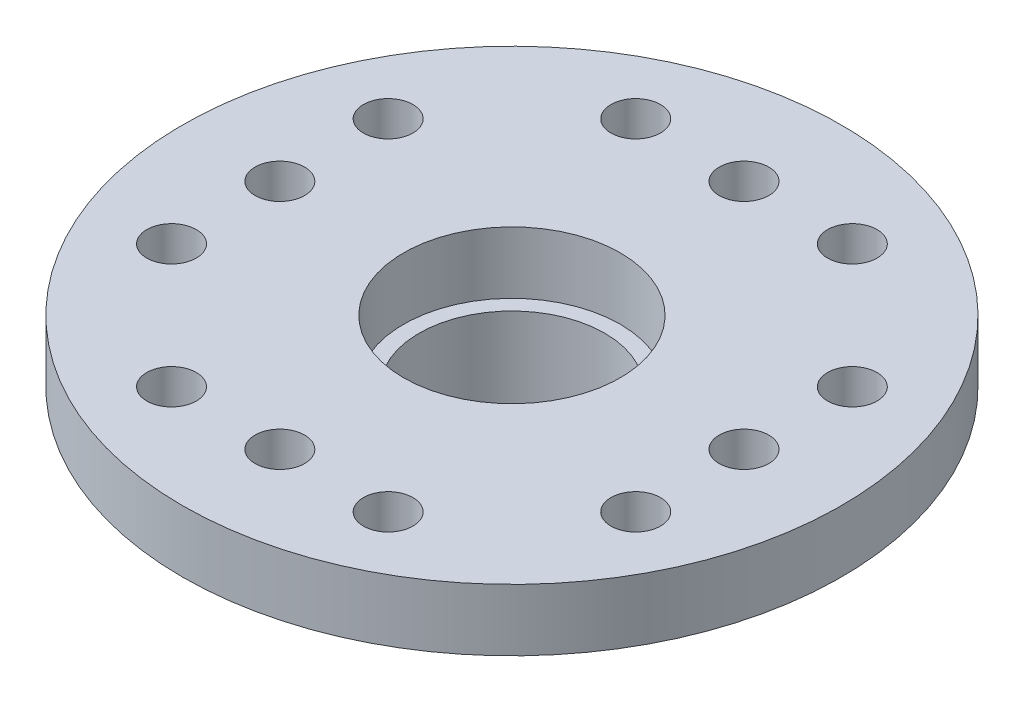
SolidWorks part; units mm, degrees
ref_plane "Спереди" through (0, 0, 0) normal (0, 0, 1) x (1, 0, 0)
ref_plane "Сверху" through (0, 0, 0) normal (0, 1, 0) x (1, 0, 0)
ref_plane "Справа" through (0, 0, 0) normal (1, 0, 0) x (0, 0, -1)
sketch "Эскиз1" plane through (0, 0, 0) normal (0, 1, 0) x (1, 0, 0)
  circle A0 centre (0, 0) radius 10.65
  circle A1 centre (0, 0) radius 3.5
  dimension "D1" = 21.3
  dimension "D2" = 7
extrude "Бобышка-Вытянуть1" add sketch "Эскиз1" along normal blind 2
sketch "Эскиз2" plane through (0, 0, 0) normal (0, -1, 0) x (1, 0, 0)
  circle A0 centre (0, 0) radius 4.3
  circle A1 centre (0, 0) radius 3
  dimension "D1" = 8.6
  dimension "D2" = 6
extrude "Бобышка-Вытянуть2" add sketch "Эскиз2" along normal blind 3.8
fillet "Скругление1" radius 1 1 edges at (0, 0, 4.3)
sketch "Эскиз3" plane through (0, 2, 0) normal (0, 1, 0) x (1, 0, 0)
  line L0 (-7.5, 7.5) -> (7.5, 7.5) construction
  line L1 (7.5, 7.5) -> (7.5, -7.5) construction
  line L2 (7.5, -7.5) -> (-7.5, -7.5) construction
  line L3 (-7.5, -7.5) -> (-7.5, 7.5) construction
  line L4 (0, 0) -> (0, 7.5) construction
  line L5 (-7.5, 0) -> (0, 0) construction
  line L6 (-7.5, 3.5) -> (7.5, 3.5) construction
  line L8 (-7.5, -3.5) -> (7.5, -3.5) construction
  line L10 (3.5, 7.5) -> (3.5, -7.5) construction
  line L12 (-3.5, 7.5) -> (-3.5, -7.5) construction
  circle A0 centre (-3.5, 7.5) radius 0.8
  circle A1 centre (0, 7.5) radius 0.8
  circle A2 centre (3.5, 7.5) radius 0.8
  circle A3 centre (7.5, 3.5) radius 0.8
  circle A4 centre (7.5, 0) radius 0.8
  circle A5 centre (7.5, -3.5) radius 0.8
  circle A6 centre (3.5, -7.5) radius 0.8
  circle A7 centre (0, -7.5) radius 0.8
  circle A8 centre (-3.5, -7.5) radius 0.8
  circle A9 centre (-7.5, -3.5) radius 0.8
  circle A10 centre (-7.5, 0) radius 0.8
  circle A11 centre (-7.5, 3.5) radius 0.8
  dimension "D6" = 1.6
  dimension "D1" = 15
  dimension "D2" = 7
  dimension "D3" = 7
  dimension "D4" = 3.5
  dimension "D5" = 3.5
extrude "Вырез-Вытянуть1" cut sketch "Эскиз3" against normal up to next
